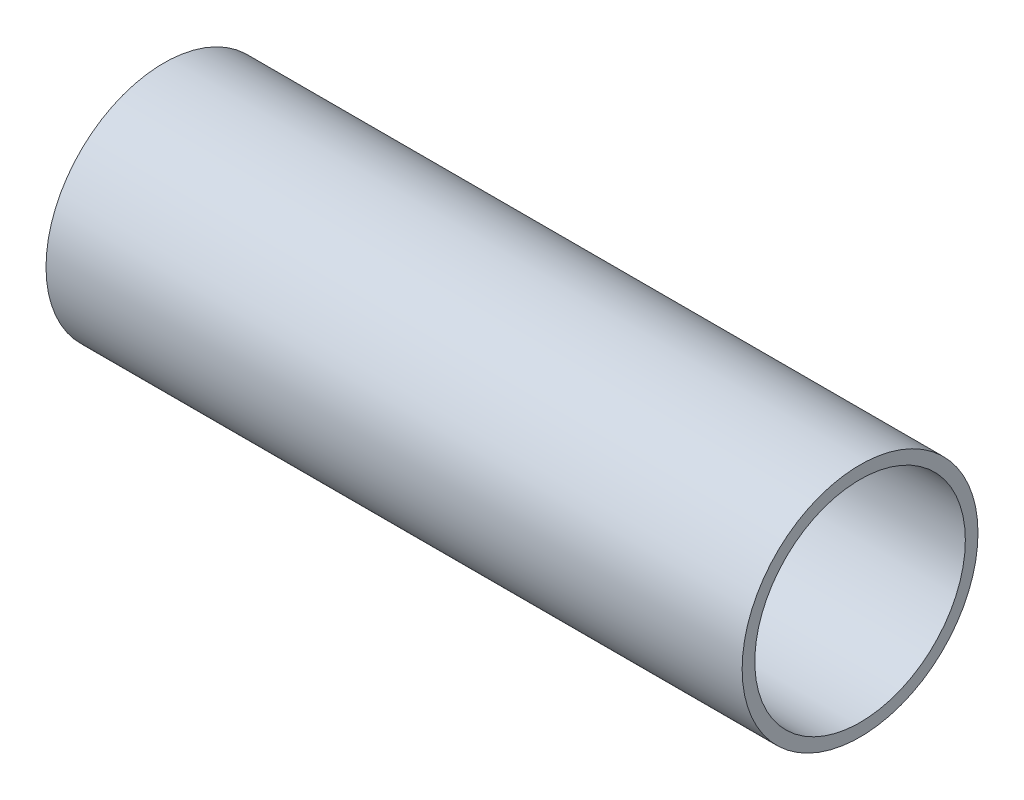
SolidWorks part; units mm, degrees
material "Acrylic (Medium-high impact)"
ref_plane "Front Plane" through (0, 0, 0) normal (0, 0, 1) x (1, 0, 0)
ref_plane "Top Plane" through (0, 0, 0) normal (0, 1, 0) x (1, 0, 0)
ref_plane "Right Plane" through (0, 0, 0) normal (1, 0, 0) x (0, 0, -1)
sketch "Sketch2" plane through (0, 0, 0) normal (1, 0, 0) x (0, 0, -1)
  circle A0 centre (0, 0) radius 93.1728
  dimension "D1" = 186.3457
extrude "Boss-Extrude1" add sketch "Sketch2" along normal blind 550
sketch "Sketch3" plane through (550, 0, 0) normal (1, 0, 0) x (0, 0, -1)
  circle A0 centre (0, 0) radius 83.1728
  circle A1 centre (0, 0) radius 93.1728 construction
  dimension "D1" = 10
extrude "Cut-Extrude1" cut sketch "Sketch3" against normal through all
